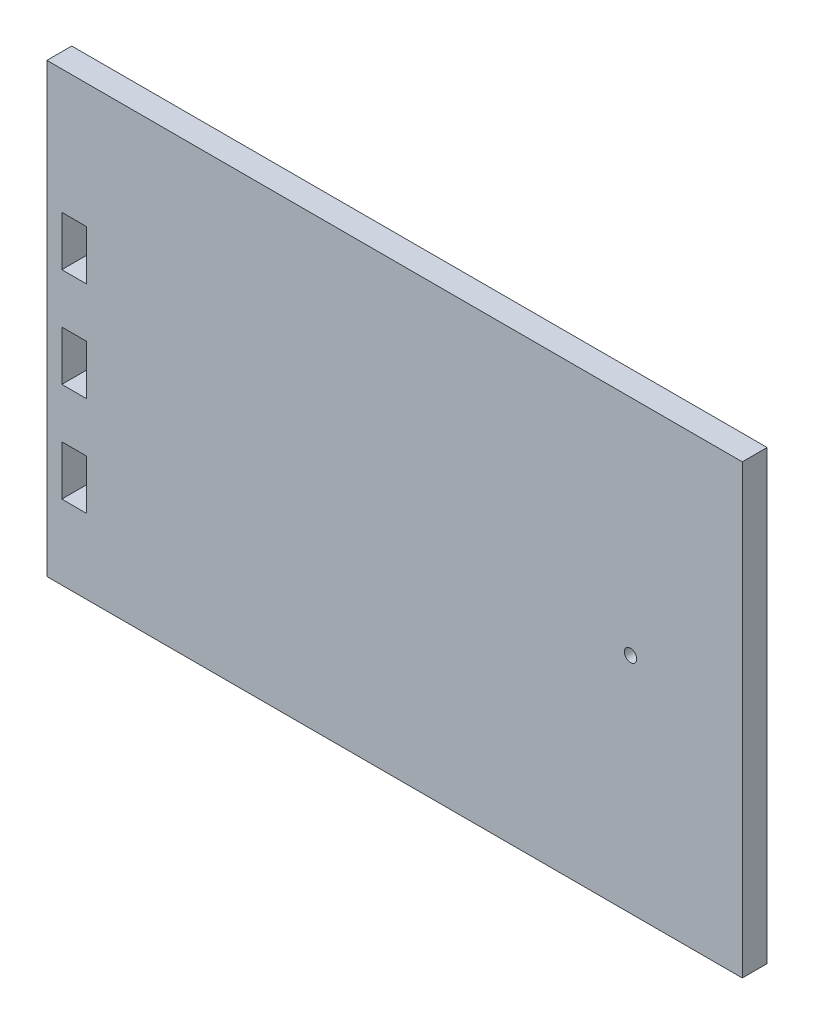
SolidWorks part; units mm, degrees
ref_plane "Front Plane" through (0, 0, 0) normal (0, 0, 1) x (1, 0, 0)
ref_plane "Top Plane" through (0, 0, 0) normal (0, 1, 0) x (1, 0, 0)
ref_plane "Right Plane" through (0, 0, 0) normal (1, 0, 0) x (0, 0, -1)
sketch "Sketch2" plane through (0, 0, 0) normal (0, 0, 1) x (1, 0, 0)
  line L1 (0, 0) -> (355.6, 0)
  line L2 (0, 0) -> (0, -228.6)
  line L3 (0, -228.6) -> (355.6, -228.6)
  line L4 (355.6, 0) -> (355.6, -228.6)
  dimension "D1" = 355.6
  dimension "D2" = 228.6
extrude "Boss-Extrude1" add sketch "Sketch2" along normal blind 12.7
sketch "Sketch3" plane through (0, 0, 12.7) normal (0, 0, 1) x (1, 0, 0)
  line L1 (355.6, -228.6) -> (355.6, 0) construction
  circle A1 centre (298.45, -114.3) radius 3.175
  dimension "D4" = 6.35
  dimension "D3" = 57.15
extrude "Cut-Extrude1" cut sketch "Sketch3" against normal blind 12.7
sketch "Sketch4" plane through (0, 0, 12.7) normal (0, 0, 1) x (1, 0, 0)
  line L1 (7.62, -63.5) -> (20.32, -63.5)
  line L2 (7.62, -63.5) -> (7.62, -88.9)
  line L3 (7.62, -88.9) -> (20.32, -88.9)
  line L4 (0, 0) -> (0, -228.6)
  line L5 (0, -228.6) -> (355.6, -228.6)
  line L6 (355.6, -228.6) -> (355.6, 0)
  line L7 (355.6, 0) -> (0, 0)
  line L8 (0, 0) -> (0, -228.6)
  line L9 (0, -228.6) -> (355.6, -228.6)
  line L10 (355.6, -228.6) -> (355.6, 0)
  line L11 (355.6, 0) -> (0, 0)
  line L12 (20.32, -63.5) -> (20.32, -88.9)
  line L13 (7.62, -114.3) -> (20.32, -114.3)
  line L14 (7.62, -114.3) -> (7.62, -139.7)
  line L15 (7.62, -139.7) -> (20.32, -139.7)
  line L16 (20.32, -114.3) -> (20.32, -139.7)
  line L17 (7.62, -165.1) -> (20.32, -165.1)
  line L18 (7.62, -165.1) -> (7.62, -190.5)
  line L19 (7.62, -190.5) -> (20.32, -190.5)
  line L20 (20.32, -165.1) -> (20.32, -190.5)
  dimension "D2" = 63.5
  dimension "D3" = 7.62
  dimension "D4" = 25.4
  dimension "D5" = 12.7
  dimension "D6" = 12.7
  dimension "D7" = 25.4
  dimension "D8" = 25.4
  dimension "D9" = 25.4
  dimension "D10" = 25.4
  dimension "D1" = 0
extrude "Cut-Extrude2" cut sketch "Sketch4" against normal through all contours L2 L1 L12 L3 | L14 L13 L16 L15 | L18 L17 L20 L19
